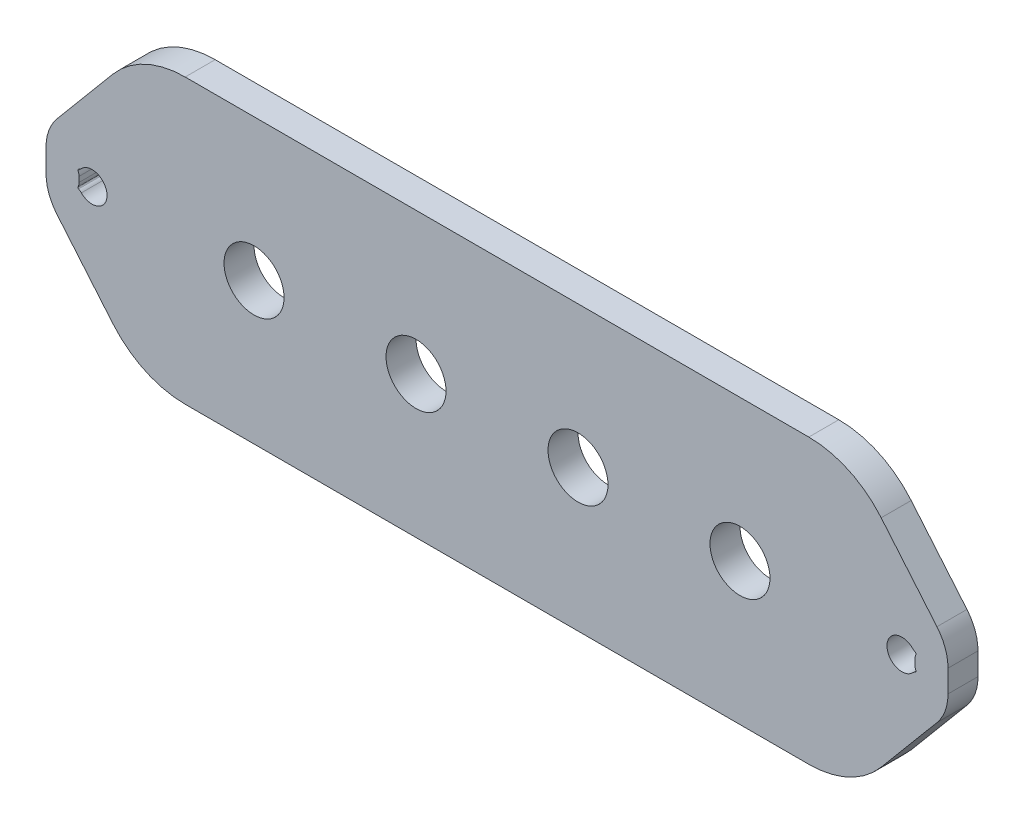
SolidWorks part; units mm, degrees
ref_plane "Front Plane" through (0, 0, 0) normal (0, 0, 1) x (1, 0, 0)
ref_plane "Top Plane" through (0, 0, 0) normal (0, 1, 0) x (1, 0, 0)
ref_plane "Right Plane" through (0, 0, 0) normal (1, 0, 0) x (0, 0, -1)
sketch "Sketch1" plane through (0, 0, 0) normal (0, 0, 1) x (1, 0, 0)
  line L0 (-85.725, 0) -> (85.725, 0) construction
  line L1 (-85.725, 30) -> (85.725, 30)
  line L2 (-85.725, -30) -> (85.725, -30)
  line L3 (0, 30) -> (0, -30) construction
  line L4 (-75.3362, 30) -> (-95.4746, 6)
  line L5 (-95.4746, 6) -> (-95.4746, -6)
  line L6 (-95.4746, -6) -> (-75.3362, -30)
  line L7 (-88.4746, -0.7777) -> (-88.4746, -1.5875) construction
  line L8 (-88.4746, -0.7777) -> (-88.4746, 0.7777) construction
  line L9 (-88.4746, 1.5875) -> (-88.4746, 0.7777) construction
  line L13 (88.4746, 1.3375) -> (88.4746, -1.3375)
  line L14 (-88.4746, 1.3375) -> (-88.4746, -1.3375)
  line L15 (95.4746, -6) -> (75.3362, -30)
  line L16 (95.4746, 6) -> (95.4746, -6)
  line L17 (75.3362, 30) -> (95.4746, 6)
  arc A0 (-85.725, 30) -> (-85.725, -30) centre (-85.725, 0) ccw
  arc A1 (85.725, -30) -> (85.725, 30) centre (85.725, 0) ccw
  arc A5 (-88.4746, -1.5875) -> (-88.4746, 1.5875) centre (-85.725, 0) ccw construction
  circle A6 centre (-88.4746, 1.5875) radius 0.25 construction
  circle A7 centre (-88.4746, -1.5875) radius 0.25 construction
  arc A11 (88.4746, -1.3375) -> (88.3412, -1.7989) centre (88.4746, -1.5875) cw
  arc A12 (88.3412, 1.7989) -> (88.4746, 1.3375) centre (88.4746, 1.5875) cw
  arc A13 (88.3412, 1.7989) -> (88.3412, -1.7989) centre (85.725, 0) ccw
  arc A14 (-88.3412, 1.7989) -> (-88.3412, -1.7989) centre (-85.725, 0) cw
  arc A15 (-88.3412, 1.7989) -> (-88.4746, 1.3375) centre (-88.4746, 1.5875) ccw
  arc A16 (-88.3412, -1.7989) -> (-88.4746, -1.3375) centre (-88.4746, -1.5875) cw
  circle A17 centre (51.435, 0) radius 6.35
  circle A18 centre (17.145, 0) radius 6.35
  circle A19 centre (-17.145, 0) radius 6.35
  circle A20 centre (-51.435, 0) radius 6.35
  point P3 (0, 0)
  point P37 (51.435, 0)
  point P38 (-95.4746, 0)
  point P39 (85.725, 0)
  point P40 (17.145, 0)
  point P41 (-17.145, 0)
  point P46 (-51.435, 0)
  dimension "D2" = 0.5
  dimension "D4" = 0.5
  dimension "D9" = 12.7
  dimension "D1" = 171.45
  dimension "D3" = 60
  dimension "D5" = 7
  dimension "D6" = 220
  dimension "D7" = 12
  dimension "D8" = 5
extrude "Boss-Extrude1" add sketch "Sketch1" along normal mid plane 6.35 contours L2 A1 L1 A0 L4 L5 L6 A13 A12 L13 A11 A14 A16 L14 A15
fillet "Fillet1" radius 2 8 edges at (-88.3412, 1.7989, 0) (88.3412, -1.7989, 0) (88.4746, -1.3375, 0) (88.4746, 1.3375, 0) (88.3412, 1.7989, 0) (-88.3412, -1.7989, 0) (-88.4746, -1.3375, 0) (-88.4746, 1.3375, 0)
fillet "Fillet2" radius 10 4 edges at (-95.4746, -6, 0) (-95.4746, 6, 0) (95.4746, -6, 0) (95.4746, 6, 0)
fillet "Fillet3" radius 20 4 edges at (-75.3362, 30, 0) (-75.3362, -30, 0) (75.3362, -30, 0) (75.3362, 30, 0)
